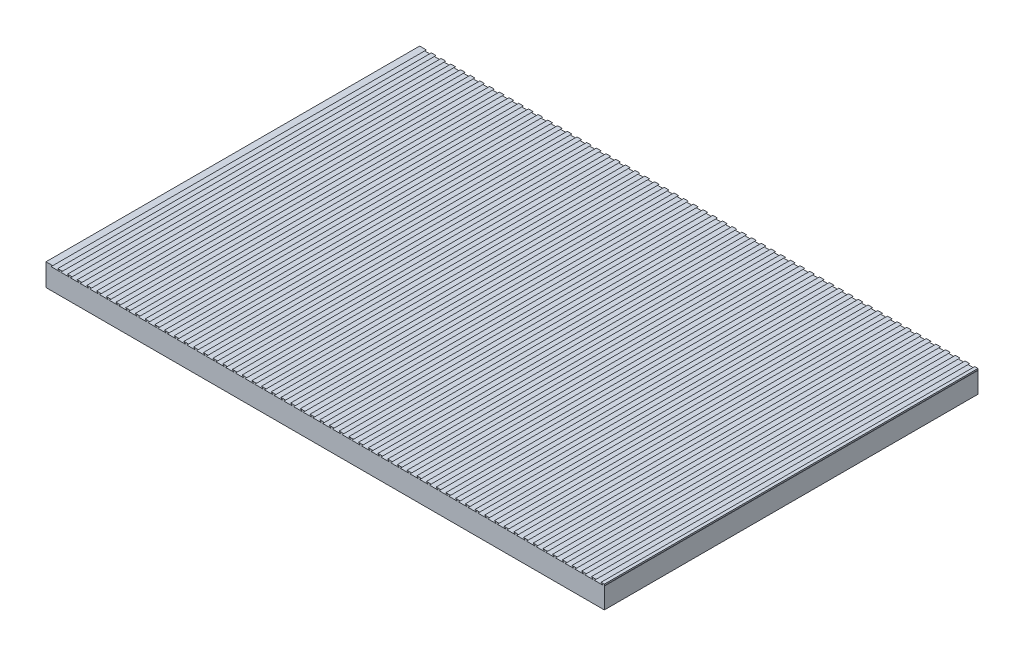
SolidWorks part; units mm, degrees
material "Alumina"
ref_plane "Front Plane" through (0, 0, 0) normal (0, 0, 1) x (1, 0, 0)
ref_plane "Top Plane" through (0, 0, 0) normal (0, 1, 0) x (1, 0, 0)
ref_plane "Right Plane" through (0, 0, 0) normal (1, 0, 0) x (0, 0, -1)
sketch "Sketch1" plane through (0, 0, 0) normal (0, 1, 0) x (1, 0, 0)
  line L1 (0, 0) -> (760.1, 0)
  line L2 (0, 0) -> (0, 508.64)
  line L3 (0, 508.64) -> (760.1, 508.64)
  line L4 (760.1, 0) -> (760.1, 508.64)
  dimension "D1" = 760.1
  dimension "D2" = 508.64
extrude "Boss-Extrude1" add sketch "Sketch1" along normal blind 30.48
sketch "Sketch2" plane through (0, 0, 0) normal (0, 0, 1) x (1, 0, 0)
  line L0 (782.1092, 30.48) -> (784.3952, 28.194)
  line L1 (0, 30.48) -> (760.1, 30.48) construction
  line L2 (784.3952, 28.194) -> (772.9652, 28.194)
  line L3 (772.9652, 28.194) -> (775.2512, 30.48)
  line L4 (775.2512, 30.48) -> (782.1092, 30.48)
  line L5 (762.0432, 30.48) -> (768.9012, 30.48)
  line L6 (768.9012, 30.48) -> (771.1872, 28.194)
  line L7 (771.1872, 28.194) -> (759.7572, 28.194)
  line L8 (759.7572, 28.194) -> (762.0432, 30.48)
  line L9 (748.8352, 30.48) -> (755.6932, 30.48)
  line L10 (755.6932, 30.48) -> (757.9792, 28.194)
  line L11 (757.9792, 28.194) -> (746.5492, 28.194)
  line L12 (746.5492, 28.194) -> (748.8352, 30.48)
  line L13 (735.6272, 30.48) -> (742.4852, 30.48)
  line L14 (742.4852, 30.48) -> (744.7712, 28.194)
  line L15 (744.7712, 28.194) -> (733.3412, 28.194)
  line L16 (733.3412, 28.194) -> (735.6272, 30.48)
  line L17 (722.4192, 30.48) -> (729.2772, 30.48)
  line L18 (729.2772, 30.48) -> (731.5632, 28.194)
  line L19 (731.5632, 28.194) -> (720.1332, 28.194)
  line L20 (720.1332, 28.194) -> (722.4192, 30.48)
  line L21 (709.2112, 30.48) -> (716.0692, 30.48)
  line L22 (716.0692, 30.48) -> (718.3552, 28.194)
  line L23 (718.3552, 28.194) -> (706.9252, 28.194)
  line L24 (706.9252, 28.194) -> (709.2112, 30.48)
  line L25 (696.0032, 30.48) -> (702.8612, 30.48)
  line L26 (702.8612, 30.48) -> (705.1472, 28.194)
  line L27 (705.1472, 28.194) -> (693.7172, 28.194)
  line L28 (693.7172, 28.194) -> (696.0032, 30.48)
  line L29 (682.7952, 30.48) -> (689.6532, 30.48)
  line L30 (689.6532, 30.48) -> (691.9392, 28.194)
  line L31 (691.9392, 28.194) -> (680.5092, 28.194)
  line L32 (680.5092, 28.194) -> (682.7952, 30.48)
  line L33 (669.5872, 30.48) -> (676.4452, 30.48)
  line L34 (676.4452, 30.48) -> (678.7312, 28.194)
  line L35 (678.7312, 28.194) -> (667.3012, 28.194)
  line L36 (667.3012, 28.194) -> (669.5872, 30.48)
  line L37 (656.3792, 30.48) -> (663.2372, 30.48)
  line L38 (663.2372, 30.48) -> (665.5232, 28.194)
  line L39 (665.5232, 28.194) -> (654.0932, 28.194)
  line L40 (654.0932, 28.194) -> (656.3792, 30.48)
  line L41 (643.1712, 30.48) -> (650.0292, 30.48)
  line L42 (650.0292, 30.48) -> (652.3152, 28.194)
  line L43 (652.3152, 28.194) -> (640.8852, 28.194)
  line L44 (640.8852, 28.194) -> (643.1712, 30.48)
  line L45 (629.9632, 30.48) -> (636.8212, 30.48)
  line L46 (636.8212, 30.48) -> (639.1072, 28.194)
  line L47 (639.1072, 28.194) -> (627.6772, 28.194)
  line L48 (627.6772, 28.194) -> (629.9632, 30.48)
  line L49 (616.7552, 30.48) -> (623.6132, 30.48)
  line L50 (623.6132, 30.48) -> (625.8992, 28.194)
  line L51 (625.8992, 28.194) -> (614.4692, 28.194)
  line L52 (614.4692, 28.194) -> (616.7552, 30.48)
  line L53 (603.5472, 30.48) -> (610.4052, 30.48)
  line L54 (610.4052, 30.48) -> (612.6912, 28.194)
  line L55 (612.6912, 28.194) -> (601.2612, 28.194)
  line L56 (601.2612, 28.194) -> (603.5472, 30.48)
  line L57 (590.3392, 30.48) -> (597.1972, 30.48)
  line L58 (597.1972, 30.48) -> (599.4832, 28.194)
  line L59 (599.4832, 28.194) -> (588.0532, 28.194)
  line L60 (588.0532, 28.194) -> (590.3392, 30.48)
  line L61 (577.1312, 30.48) -> (583.9892, 30.48)
  line L62 (583.9892, 30.48) -> (586.2752, 28.194)
  line L63 (586.2752, 28.194) -> (574.8452, 28.194)
  line L64 (574.8452, 28.194) -> (577.1312, 30.48)
  line L65 (563.9232, 30.48) -> (570.7812, 30.48)
  line L66 (570.7812, 30.48) -> (573.0672, 28.194)
  line L67 (573.0672, 28.194) -> (561.6372, 28.194)
  line L68 (561.6372, 28.194) -> (563.9232, 30.48)
  line L69 (550.7152, 30.48) -> (557.5732, 30.48)
  line L70 (557.5732, 30.48) -> (559.8592, 28.194)
  line L71 (559.8592, 28.194) -> (548.4292, 28.194)
  line L72 (548.4292, 28.194) -> (550.7152, 30.48)
  line L73 (537.5072, 30.48) -> (544.3652, 30.48)
  line L74 (544.3652, 30.48) -> (546.6512, 28.194)
  line L75 (546.6512, 28.194) -> (535.2212, 28.194)
  line L76 (535.2212, 28.194) -> (537.5072, 30.48)
  line L77 (524.2992, 30.48) -> (531.1572, 30.48)
  line L78 (531.1572, 30.48) -> (533.4432, 28.194)
  line L79 (533.4432, 28.194) -> (522.0132, 28.194)
  line L80 (522.0132, 28.194) -> (524.2992, 30.48)
  line L81 (511.0912, 30.48) -> (517.9492, 30.48)
  line L82 (517.9492, 30.48) -> (520.2352, 28.194)
  line L83 (520.2352, 28.194) -> (508.8052, 28.194)
  line L84 (508.8052, 28.194) -> (511.0912, 30.48)
  line L85 (497.8832, 30.48) -> (504.7412, 30.48)
  line L86 (504.7412, 30.48) -> (507.0272, 28.194)
  line L87 (507.0272, 28.194) -> (495.5972, 28.194)
  line L88 (495.5972, 28.194) -> (497.8832, 30.48)
  line L89 (484.6752, 30.48) -> (491.5332, 30.48)
  line L90 (491.5332, 30.48) -> (493.8192, 28.194)
  line L91 (493.8192, 28.194) -> (482.3892, 28.194)
  line L92 (482.3892, 28.194) -> (484.6752, 30.48)
  line L93 (471.4672, 30.48) -> (478.3252, 30.48)
  line L94 (478.3252, 30.48) -> (480.6112, 28.194)
  line L95 (480.6112, 28.194) -> (469.1812, 28.194)
  line L96 (469.1812, 28.194) -> (471.4672, 30.48)
  line L97 (458.2592, 30.48) -> (465.1172, 30.48)
  line L98 (465.1172, 30.48) -> (467.4032, 28.194)
  line L99 (467.4032, 28.194) -> (455.9732, 28.194)
  line L100 (455.9732, 28.194) -> (458.2592, 30.48)
  line L101 (445.0512, 30.48) -> (451.9092, 30.48)
  line L102 (451.9092, 30.48) -> (454.1952, 28.194)
  line L103 (454.1952, 28.194) -> (442.7652, 28.194)
  line L104 (442.7652, 28.194) -> (445.0512, 30.48)
  line L105 (431.8432, 30.48) -> (438.7012, 30.48)
  line L106 (438.7012, 30.48) -> (440.9872, 28.194)
  line L107 (440.9872, 28.194) -> (429.5572, 28.194)
  line L108 (429.5572, 28.194) -> (431.8432, 30.48)
  line L109 (418.6352, 30.48) -> (425.4932, 30.48)
  line L110 (425.4932, 30.48) -> (427.7792, 28.194)
  line L111 (427.7792, 28.194) -> (416.3492, 28.194)
  line L112 (416.3492, 28.194) -> (418.6352, 30.48)
  line L113 (405.4272, 30.48) -> (412.2852, 30.48)
  line L114 (412.2852, 30.48) -> (414.5712, 28.194)
  line L115 (414.5712, 28.194) -> (403.1412, 28.194)
  line L116 (403.1412, 28.194) -> (405.4272, 30.48)
  line L117 (392.2192, 30.48) -> (399.0772, 30.48)
  line L118 (399.0772, 30.48) -> (401.3632, 28.194)
  line L119 (401.3632, 28.194) -> (389.9332, 28.194)
  line L120 (389.9332, 28.194) -> (392.2192, 30.48)
  line L121 (379.0112, 30.48) -> (385.8692, 30.48)
  line L122 (385.8692, 30.48) -> (388.1552, 28.194)
  line L123 (388.1552, 28.194) -> (376.7252, 28.194)
  line L124 (376.7252, 28.194) -> (379.0112, 30.48)
  line L125 (365.8032, 30.48) -> (372.6612, 30.48)
  line L126 (372.6612, 30.48) -> (374.9472, 28.194)
  line L127 (374.9472, 28.194) -> (363.5172, 28.194)
  line L128 (363.5172, 28.194) -> (365.8032, 30.48)
  line L129 (352.5952, 30.48) -> (359.4532, 30.48)
  line L130 (359.4532, 30.48) -> (361.7392, 28.194)
  line L131 (361.7392, 28.194) -> (350.3092, 28.194)
  line L132 (350.3092, 28.194) -> (352.5952, 30.48)
  line L133 (339.3872, 30.48) -> (346.2452, 30.48)
  line L134 (346.2452, 30.48) -> (348.5312, 28.194)
  line L135 (348.5312, 28.194) -> (337.1012, 28.194)
  line L136 (337.1012, 28.194) -> (339.3872, 30.48)
  line L137 (326.1792, 30.48) -> (333.0372, 30.48)
  line L138 (333.0372, 30.48) -> (335.3232, 28.194)
  line L139 (335.3232, 28.194) -> (323.8932, 28.194)
  line L140 (323.8932, 28.194) -> (326.1792, 30.48)
  line L141 (312.9712, 30.48) -> (319.8292, 30.48)
  line L142 (319.8292, 30.48) -> (322.1152, 28.194)
  line L143 (322.1152, 28.194) -> (310.6852, 28.194)
  line L144 (310.6852, 28.194) -> (312.9712, 30.48)
  line L145 (299.7632, 30.48) -> (306.6212, 30.48)
  line L146 (306.6212, 30.48) -> (308.9072, 28.194)
  line L147 (308.9072, 28.194) -> (297.4772, 28.194)
  line L148 (297.4772, 28.194) -> (299.7632, 30.48)
  line L149 (286.5552, 30.48) -> (293.4132, 30.48)
  line L150 (293.4132, 30.48) -> (295.6992, 28.194)
  line L151 (295.6992, 28.194) -> (284.2692, 28.194)
  line L152 (284.2692, 28.194) -> (286.5552, 30.48)
  line L153 (273.3472, 30.48) -> (280.2052, 30.48)
  line L154 (280.2052, 30.48) -> (282.4912, 28.194)
  line L155 (282.4912, 28.194) -> (271.0612, 28.194)
  line L156 (271.0612, 28.194) -> (273.3472, 30.48)
  line L157 (260.1392, 30.48) -> (266.9972, 30.48)
  line L158 (266.9972, 30.48) -> (269.2832, 28.194)
  line L159 (269.2832, 28.194) -> (257.8532, 28.194)
  line L160 (257.8532, 28.194) -> (260.1392, 30.48)
  line L161 (246.9312, 30.48) -> (253.7892, 30.48)
  line L162 (253.7892, 30.48) -> (256.0752, 28.194)
  line L163 (256.0752, 28.194) -> (244.6452, 28.194)
  line L164 (244.6452, 28.194) -> (246.9312, 30.48)
  line L165 (233.7232, 30.48) -> (240.5812, 30.48)
  line L166 (240.5812, 30.48) -> (242.8672, 28.194)
  line L167 (242.8672, 28.194) -> (231.4372, 28.194)
  line L168 (231.4372, 28.194) -> (233.7232, 30.48)
  line L169 (220.5152, 30.48) -> (227.3732, 30.48)
  line L170 (227.3732, 30.48) -> (229.6592, 28.194)
  line L171 (229.6592, 28.194) -> (218.2292, 28.194)
  line L172 (218.2292, 28.194) -> (220.5152, 30.48)
  line L173 (207.3072, 30.48) -> (214.1652, 30.48)
  line L174 (214.1652, 30.48) -> (216.4512, 28.194)
  line L175 (216.4512, 28.194) -> (205.0212, 28.194)
  line L176 (205.0212, 28.194) -> (207.3072, 30.48)
  line L177 (194.0992, 30.48) -> (200.9572, 30.48)
  line L178 (200.9572, 30.48) -> (203.2432, 28.194)
  line L179 (203.2432, 28.194) -> (191.8132, 28.194)
  line L180 (191.8132, 28.194) -> (194.0992, 30.48)
  line L181 (180.8912, 30.48) -> (187.7492, 30.48)
  line L182 (187.7492, 30.48) -> (190.0352, 28.194)
  line L183 (190.0352, 28.194) -> (178.6052, 28.194)
  line L184 (178.6052, 28.194) -> (180.8912, 30.48)
  line L185 (167.6832, 30.48) -> (174.5412, 30.48)
  line L186 (174.5412, 30.48) -> (176.8272, 28.194)
  line L187 (176.8272, 28.194) -> (165.3972, 28.194)
  line L188 (165.3972, 28.194) -> (167.6832, 30.48)
  line L189 (154.4752, 30.48) -> (161.3332, 30.48)
  line L190 (161.3332, 30.48) -> (163.6192, 28.194)
  line L191 (163.6192, 28.194) -> (152.1892, 28.194)
  line L192 (152.1892, 28.194) -> (154.4752, 30.48)
  line L193 (141.2672, 30.48) -> (148.1252, 30.48)
  line L194 (148.1252, 30.48) -> (150.4112, 28.194)
  line L195 (150.4112, 28.194) -> (138.9812, 28.194)
  line L196 (138.9812, 28.194) -> (141.2672, 30.48)
  line L197 (128.0592, 30.48) -> (134.9172, 30.48)
  line L198 (134.9172, 30.48) -> (137.2032, 28.194)
  line L199 (137.2032, 28.194) -> (125.7732, 28.194)
  line L200 (125.7732, 28.194) -> (128.0592, 30.48)
  line L201 (114.8512, 30.48) -> (121.7092, 30.48)
  line L202 (121.7092, 30.48) -> (123.9952, 28.194)
  line L203 (123.9952, 28.194) -> (112.5652, 28.194)
  line L204 (112.5652, 28.194) -> (114.8512, 30.48)
  line L205 (101.6432, 30.48) -> (108.5012, 30.48)
  line L206 (108.5012, 30.48) -> (110.7872, 28.194)
  line L207 (110.7872, 28.194) -> (99.3572, 28.194)
  line L208 (99.3572, 28.194) -> (101.6432, 30.48)
  line L209 (88.4352, 30.48) -> (95.2932, 30.48)
  line L210 (95.2932, 30.48) -> (97.5792, 28.194)
  line L211 (97.5792, 28.194) -> (86.1492, 28.194)
  line L212 (86.1492, 28.194) -> (88.4352, 30.48)
  line L213 (75.2272, 30.48) -> (82.0852, 30.48)
  line L214 (82.0852, 30.48) -> (84.3712, 28.194)
  line L215 (84.3712, 28.194) -> (72.9412, 28.194)
  line L216 (72.9412, 28.194) -> (75.2272, 30.48)
  line L217 (62.0192, 30.48) -> (68.8772, 30.48)
  line L218 (68.8772, 30.48) -> (71.1632, 28.194)
  line L219 (71.1632, 28.194) -> (59.7332, 28.194)
  line L220 (59.7332, 28.194) -> (62.0192, 30.48)
  line L221 (48.8112, 30.48) -> (55.6692, 30.48)
  line L222 (55.6692, 30.48) -> (57.9552, 28.194)
  line L223 (57.9552, 28.194) -> (46.5252, 28.194)
  line L224 (46.5252, 28.194) -> (48.8112, 30.48)
  line L225 (35.6032, 30.48) -> (42.4612, 30.48)
  line L226 (42.4612, 30.48) -> (44.7472, 28.194)
  line L227 (44.7472, 28.194) -> (33.3172, 28.194)
  line L228 (33.3172, 28.194) -> (35.6032, 30.48)
  line L229 (22.3952, 30.48) -> (29.2532, 30.48)
  line L230 (29.2532, 30.48) -> (31.5392, 28.194)
  line L231 (31.5392, 28.194) -> (20.1092, 28.194)
  line L232 (20.1092, 28.194) -> (22.3952, 30.48)
  line L233 (9.1872, 30.48) -> (16.0452, 30.48)
  line L234 (16.0452, 30.48) -> (18.3312, 28.194)
  line L235 (18.3312, 28.194) -> (6.9012, 28.194)
  line L236 (6.9012, 28.194) -> (9.1872, 30.48)
  dimension "D1" = 11.43
  dimension "D2" = 45
  dimension "D3" = 45
  dimension "D4" = 2.286
  dimension "D5" = 59
extrude "Cut-Extrude1" cut sketch "Sketch2" against normal through all
